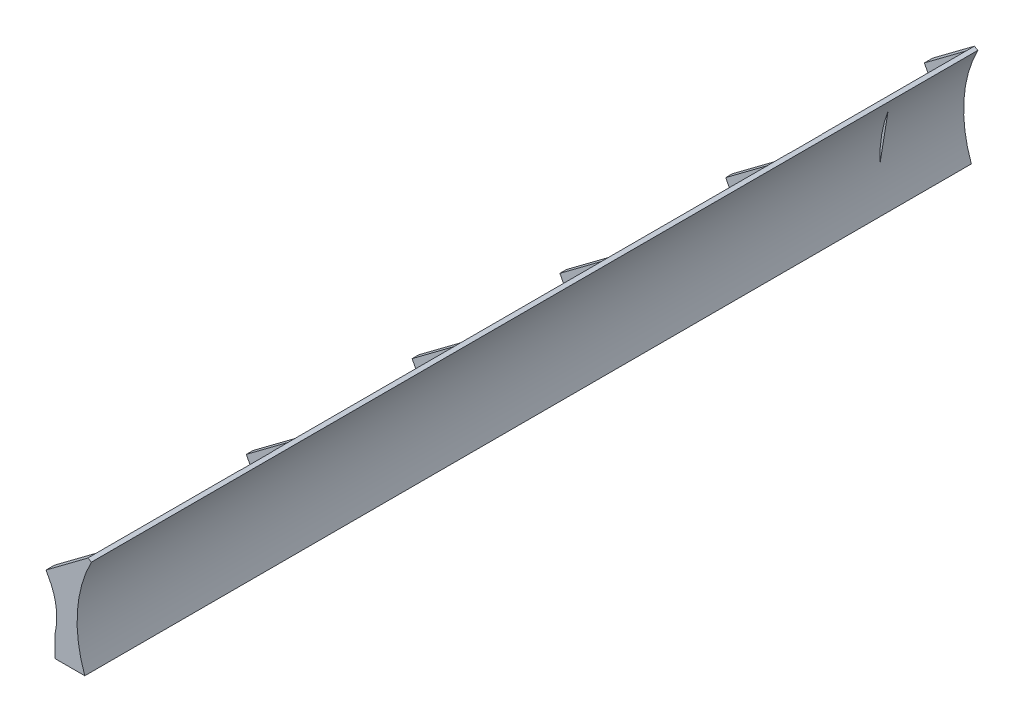
SolidWorks part; units mm, degrees
ref_plane "Plan de face" through (0, 0, 0) normal (0, 0, 1) x (1, 0, 0)
ref_plane "Plan de dessus" through (0, 0, 0) normal (0, 1, 0) x (1, 0, 0)
ref_plane "Plan de droite" through (0, 0, 0) normal (1, 0, 0) x (0, 0, -1)
sketch "Esquisse1" plane through (0, 0, 0) normal (0, 0, 1) x (1, 0, 0)
  line L5 (16.064, 30.399) -> (13.815, 31.399)
  line L9 (-5.9851, -17.839) -> (-5.9851, -31.601)
  line L10 (-8.464, 6.3989) -> (-11.6132, 12.3881)
  line L11 (-5.9851, -31.601) -> (12.0149, -31.601)
  line L19 (13.815, 31.399) -> (-11.6132, 12.3881)
  arc A1 (16.064, 30.399) -> (12.0149, -31.601) centre (84.015, -5.1709) ccw
  arc A2 (-8.464, 6.3989) -> (-5.9851, -17.839) centre (-43.8268, -9.4635) cw
  dimension "D1" = 63
  dimension "D2" = 62
  dimension "D3" = 18
extrude "Boss.-Extru.1" add sketch "Esquisse1" along normal blind 270
ref_plane "Plan1" through (0, 0, 265) normal (0, 0, 1) x (1, 0, 0)
sketch "Esquisse3" plane through (0, 0, 265) normal (0, 0, 1) x (1, 0, 0)
  line L10 (-8.464, 6.3989) -> (-11.6132, 12.3881)
  line L12 (-5.9851, -17.839) -> (3.6658, -17.839)
  line L15 (-5.9851, -17.839) -> (-5.9851, -31.601) construction
  line L16 (16.064, 30.399) -> (13.815, 31.399) construction
  line L19 (13.815, 31.399) -> (-11.6132, 12.3881)
  arc A2 (-8.464, 6.3989) -> (-5.9851, -17.839) centre (-43.8268, -9.4635) cw
  arc A3 (13.815, 31.399) -> (3.6658, -17.839) centre (78.6474, -7.6296) ccw
extrude "Enlèv. mat.-Extru.4" cut sketch "Esquisse3" against normal blind 26
ref_plane "Plan2" through (0, 0, 239) normal (0, 0, 1) x (1, 0, 0)
sketch "Esquisse5" plane through (0, 0, 239) normal (0, 0, 1) x (1, 0, 0)
  line L10 (-8.464, 6.3989) -> (-11.6132, 12.3881)
  line L17 (-5.9851, -17.839) -> (-5.9851, -27.2525)
  line L19 (13.815, 31.399) -> (-11.6132, 12.3881)
  line L20 (-5.9851, -17.839) -> (3.6658, -17.839) construction
  line L21 (-5.9851, -17.839) -> (-5.9851, -31.601) construction
  line L22 (-5.9851, -27.2525) -> (4.2805, -27.2525)
  line L23 (4.2805, -22.6598) -> (4.2805, -27.2525)
  line L24 (13.815, 31.399) -> (-11.6132, 12.3881) construction
  arc A2 (-8.464, 6.3989) -> (-5.9851, -17.839) centre (-43.8268, -9.4635) cw
  arc A4 (13.815, 31.399) -> (4.2805, -22.6598) centre (79.9087, -8.1284) ccw
  arc A5 (13.815, 31.399) -> (3.6658, -17.839) centre (78.6474, -7.6296) ccw construction
extrude "Enlèv. mat.-Extru.5" cut sketch "Esquisse5" against normal blind 20
ref_plane "Plan3" through (0, 0, 219) normal (0, 0, 1) x (1, 0, 0)
sketch "Esquisse6" plane through (0, 0, 219) normal (0, 0, 1) x (1, 0, 0)
  line L10 (-8.464, 6.3989) -> (-11.6132, 12.3881)
  line L17 (-8.464, 6.3989) -> (7.2963, 17.5793)
  line L19 (13.815, 31.399) -> (-11.6132, 12.3881)
  arc A3 (13.815, 31.399) -> (7.2963, 17.5793) centre (78.6474, -7.6296) ccw
  arc A4 (-5.9851, -17.839) -> (-8.464, 6.3989) centre (-43.8268, -9.4635) ccw construction
extrude "Enlèv. mat.-Extru.6" cut sketch "Esquisse6" against normal blind 42
ref_plane "Plan5" through (0, 0, 177) normal (0, 0, 1) x (1, 0, 0)
sketch "Esquisse9" plane through (0, 0, 177) normal (0, 0, 1) x (1, 0, 0)
  line L0 (-8.5215, 6.1429) -> (-11.9848, 12.7294)
  line L2 (-6.0427, -18.0949) -> (-6.0427, -27.5085)
  line L5 (14.702, 32.6813) -> (-11.9848, 12.7294)
  line L7 (-6.0427, -27.5085) -> (4.2229, -27.5085)
  line L10 (4.2229, -22.9157) -> (4.2229, -27.5085)
  arc A2 (-8.5215, 6.1429) -> (-6.0427, -18.0949) centre (-43.8844, -9.7194) cw
  arc A3 (14.702, 32.6813) -> (4.2229, -22.9157) centre (79.8511, -8.3843) ccw
extrude "Enlèv. mat.-Extru.7" cut sketch "Esquisse9" against normal blind 19
ref_plane "Plan6" through (0, 0, 158) normal (0, 0, 1) x (1, 0, 0)
sketch "Esquisse10" plane through (0, 0, 158) normal (0, 0, 1) x (1, 0, 0)
  line L10 (-8.464, 6.3989) -> (-11.6132, 12.3881)
  line L12 (-5.9851, -17.839) -> (3.6658, -17.839)
  line L19 (13.815, 31.399) -> (-11.6132, 12.3881)
  arc A2 (-8.464, 6.3989) -> (-5.9851, -17.839) centre (-43.8268, -9.4635) cw
  arc A3 (13.815, 31.399) -> (3.6658, -17.839) centre (78.6474, -7.6296) ccw
extrude "Enlèv. mat.-Extru.8" cut sketch "Esquisse10" against normal blind 10
ref_plane "Plan7" through (0, 0, 144) normal (0, 0, 1) x (1, 0, 0)
sketch "Esquisse11" plane through (0, 0, 144) normal (0, 0, 1) x (1, 0, 0)
  line L10 (-8.464, 6.3989) -> (-11.6132, 12.3881)
  line L12 (-5.9851, -17.839) -> (3.6658, -17.839)
  line L19 (13.815, 31.399) -> (-11.6132, 12.3881)
  arc A2 (-8.464, 6.3989) -> (-5.9851, -17.839) centre (-43.8268, -9.4635) cw
  arc A3 (13.815, 31.399) -> (3.6658, -17.839) centre (78.6474, -7.6296) ccw
extrude "Enlèv. mat.-Extru.9" cut sketch "Esquisse11" against normal blind 10
ref_plane "Plan8" through (0, 0, 134) normal (0, 0, 1) x (1, 0, 0)
sketch "Esquisse12" plane through (0, 0, 134) normal (0, 0, 1) x (1, 0, 0)
  line L10 (-8.464, 6.3989) -> (-11.6132, 12.3881)
  line L17 (-5.9851, -17.839) -> (-5.9851, -27.2525)
  line L19 (13.815, 31.399) -> (-11.6132, 12.3881)
  line L22 (-5.9851, -27.2525) -> (4.2805, -27.2525)
  line L23 (4.2805, -22.6598) -> (4.2805, -27.2525)
  arc A2 (-8.464, 6.3989) -> (-5.9851, -17.839) centre (-43.8268, -9.4635) cw
  arc A4 (13.815, 31.399) -> (4.2805, -22.6598) centre (79.9087, -8.1284) ccw
extrude "Enlèv. mat.-Extru.10" cut sketch "Esquisse12" against normal blind 77
ref_plane "Plan9" through (0, 0, 57) normal (0, 0, 1) x (1, 0, 0)
sketch "Esquisse13" plane through (0, 0, 57) normal (0, 0, 1) x (1, 0, 0)
  line L10 (-8.464, 6.3989) -> (-11.6132, 12.3881)
  line L12 (-5.9851, -17.839) -> (3.6658, -17.839)
  line L19 (13.815, 31.399) -> (-11.6132, 12.3881)
  arc A2 (-8.464, 6.3989) -> (-5.9851, -17.839) centre (-43.8268, -9.4635) cw
  arc A3 (13.815, 31.399) -> (3.6658, -17.839) centre (78.6474, -7.6296) ccw
extrude "Enlèv. mat.-Extru.11" cut sketch "Esquisse13" against normal blind 10
ref_plane "Plan10" through (0, 0, 43) normal (0, 0, 1) x (1, 0, 0)
sketch "Esquisse14" plane through (0, 0, 43) normal (0, 0, 1) x (1, 0, 0)
  line L10 (-8.464, 6.3989) -> (-11.6132, 12.3881)
  line L12 (-5.9851, -17.839) -> (3.6658, -17.839)
  line L19 (13.815, 31.399) -> (-11.6132, 12.3881)
  arc A2 (-8.464, 6.3989) -> (-5.9851, -17.839) centre (-43.8268, -9.4635) cw
  arc A3 (13.815, 31.399) -> (3.6658, -17.839) centre (78.6474, -7.6296) ccw
extrude "Enlèv. mat.-Extru.12" cut sketch "Esquisse14" against normal blind 10
ref_plane "Plan11" through (0, 0, 33) normal (0, 0, 1) x (1, 0, 0)
sketch "Esquisse15" plane through (0, 0, 33) normal (0, 0, 1) x (1, 0, 0)
  line L10 (-8.464, 6.3989) -> (-11.6132, 12.3881)
  line L17 (-5.9851, -17.839) -> (-5.9851, -27.2525)
  line L19 (13.815, 31.399) -> (-11.6132, 12.3881)
  line L22 (-5.9851, -27.2525) -> (4.2805, -27.2525)
  line L23 (4.2805, -22.6598) -> (4.2805, -27.2525)
  arc A2 (-8.464, 6.3989) -> (-5.9851, -17.839) centre (-43.8268, -9.4635) cw
  arc A4 (13.815, 31.399) -> (4.2805, -22.6598) centre (79.9087, -8.1284) ccw
extrude "Enlèv. mat.-Extru.13" cut sketch "Esquisse15" against normal blind 37
ref_plane "MILIEU DE LA PIECE" through (0, 0, 0) normal (0, 0, -1) x (-1, 0, 0)
mirror "Symétrie1" about plane through (0, 0, 0) normal (0, 0, -1) of "Enlèv. mat.-Extru.13", "Enlèv. mat.-Extru.12", "Enlèv. mat.-Extru.11", "Enlèv. mat.-Extru.10", "Enlèv. mat.-Extru.9", "Enlèv. mat.-Extru.8", "Enlèv. mat.-Extru.7", "Enlèv. mat.-Extru.6", "Enlèv. mat.-Extru.5", "Enlèv. mat.-Extru.4", "Boss.-Extru.1"
sketch "Esquisse26" plane through (0, -31.601, 0) normal (0, -1, 0) x (1, 0, 0)
  line L0 (-24.6294, 247) -> (46.4526, 247) construction
  line L1 (-43.8268, 146) -> (43.2573, 146) construction
  line L2 (-43.8268, 148) -> (-43.8268, 144) construction
  line L3 (-43.8268, 219) -> (-43.8268, 177) construction
  line L4 (-35.8101, 45) -> (48.0491, 45) construction
  line L5 (3.0149, 277.1222) -> (3.0149, 12.5356) construction
  line L6 (-5.9851, 270) -> (12.0149, 270) construction
  line L7 (-5.9851, 270) -> (-5.9851, -270) construction
  dimension "D1" = 23
  dimension "D2" = 101
  dimension "D3" = 101
  dimension "D4" = 9
hole_wizard "Trou taraudé G1/162" positions "Esquisse3D2" profile "Esquisse27" tap size "G1/16" standard "ISO"
sketch3d "Esquisse3D2"
  line L0 (-24.6294, -31.601, 247) -> (46.4526, -31.601, 247) construction
  line L1 (3.0149, -31.601, 277.1222) -> (3.0149, -31.601, 12.5356) construction
  point P0 (3.0149, -31.601, 247)
sketch "Esquisse27" plane through (3.0149, -31.601, 247) normal (1, 0, 0) x (0, 0, -1)
  line L0 (0, 0) -> (0, 12)
  line L1 (0, 12) -> (3.3, 10.0172)
  line L2 (3.3, 10.0172) -> (3.3, 0)
  line L5 (3.3, 0) -> (0, 0)
  line L10 (0, 12) -> (-3.3, 10.0172) construction
  line L11 (0, -6.35) -> (0, 107.95) construction
  dimension "Diamètre du trou pour taraudage" = 6.6
  dimension "Profondeur du trou pour taraudage" = 12
  dimension "Angle de pointe" = 118
cosmetic thread "Filetage de perçage4"
hole_wizard "Trou taraudé G1/163" positions "Esquisse3D3" profile "Esquisse28" tap size "G1/16" standard "ISO"
sketch3d "Esquisse3D3"
  line L0 (-43.8268, -31.601, 146) -> (43.2573, -31.601, 146) construction
  point P0 (2.9502, -31.601, 146)
sketch "Esquisse28" plane through (2.9502, -31.601, 146) normal (1, 0, 0) x (0, 0, -1)
  line L0 (0, 0) -> (0, 12)
  line L1 (0, 12) -> (3.3, 10.0172)
  line L2 (3.3, 10.0172) -> (3.3, 0)
  line L5 (3.3, 0) -> (0, 0)
  line L10 (0, 12) -> (-3.3, 10.0172) construction
  line L11 (0, -6.35) -> (0, 107.95) construction
  dimension "Diamètre du trou pour taraudage" = 6.6
  dimension "Profondeur du trou pour taraudage" = 12
  dimension "Angle de pointe" = 118
cosmetic thread "Filetage de perçage5"
hole_wizard "Trou taraudé G1/164" positions "Esquisse3D4" profile "Esquisse29" tap size "G1/16" standard "ISO"
sketch3d "Esquisse3D4"
  line L0 (-35.8101, -31.601, 45) -> (48.0491, -31.601, 45) construction
  line L1 (3.0149, -31.601, 277.1222) -> (3.0149, -31.601, 12.5356) construction
  point P0 (3.0149, -31.601, 45)
sketch "Esquisse29" plane through (3.0149, -31.601, 45) normal (1, 0, 0) x (0, 0, -1)
  line L0 (0, 0) -> (0, 12)
  line L1 (0, 12) -> (3.3, 10.0172)
  line L2 (3.3, 10.0172) -> (3.3, 0)
  line L5 (3.3, 0) -> (0, 0)
  line L10 (0, 12) -> (-3.3, 10.0172) construction
  line L11 (0, -6.35) -> (0, 107.95) construction
  dimension "Diamètre du trou pour taraudage" = 6.6
  dimension "Profondeur du trou pour taraudage" = 12
  dimension "Angle de pointe" = 118
cosmetic thread "Filetage de perçage6"
mirror "Symétrie2" about plane through (0, 0, 0) normal (0, 0, -1) of "Trou taraudé G1/164", "Trou taraudé G1/163", "Trou taraudé G1/162"
cosmetic thread "Filetage de perçage7"
cosmetic thread "Filetage de perçage8"
cosmetic thread "Filetage de perçage9"
